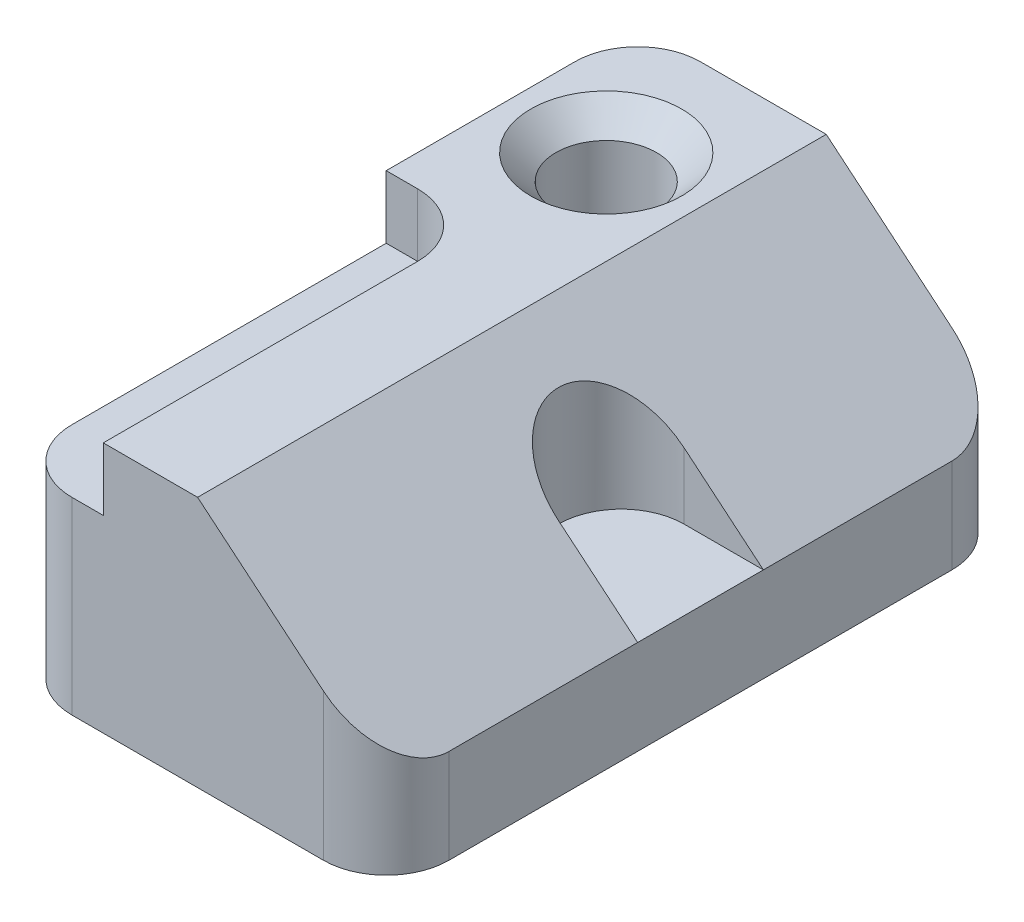
SolidWorks part; units mm, degrees
material "Plain Carbon Steel"
ref_plane "Front Plane" through (0, 0, 0) normal (0, 0, 1) x (1, 0, 0)
ref_plane "Top Plane" through (0, 0, 0) normal (0, 1, 0) x (1, 0, 0)
ref_plane "Right Plane" through (0, 0, 0) normal (1, 0, 0) x (0, 0, -1)
sketch "Sketch1" plane through (0, 0, 0) normal (0, 0, 1) x (1, 0, 0)
  line L0 (0, 0) -> (0, 50.8)
  line L1 (0, 50.8) -> (38.1, 50.8)
  line L2 (38.1, 50.8) -> (76.2, 19.05)
  line L3 (76.2, 19.05) -> (76.2, 0)
  line L4 (76.2, 0) -> (0, 0)
  dimension "D1" = 50.8
  dimension "D2" = 76.2
  dimension "D3" = 19.05
  dimension "D4" = 38.1
extrude "Boss-Extrude1" add sketch "Sketch1" along normal blind 127 contours L4 L0 L1 L2 L3
sketch "Sketch3" plane through (0, 50.8, 0) normal (0, 1, 0) x (1, 0, 0)
  line L0 (0, 0) -> (38.1, 0) construction
  line L1 (0, -127) -> (0, 0) construction
  circle A1 centre (19.05, -25.4) radius 10.16
  point P2 (18.6084, -21.3515)
  point P5 (19.05, 0)
  point P6 (0, 0)
  point P9 (0, 0)
  dimension "D1" = 20.32
  dimension "D2" = 25.4
  dimension "D3" = 19.05
extrude "Cut-Extrude1" cut sketch "Sketch3" against normal blind 127
chamfer "Chamfer1" distance 5.08 angle 45 1 edges at (19.05, 50.8, 35.56)
sketch "Sketch4" plane through (0, 50.8, 0) normal (0, 1, 0) x (1, 0, 0)
  line L1 (0, -127) -> (19.05, -127)
  line L2 (0, -127) -> (0, -50.8)
  line L3 (0, -50.8) -> (19.05, -50.8)
  line L4 (19.05, -127) -> (19.05, -50.8)
  dimension "D1" = 76.2
  dimension "D2" = 19.05
extrude "Cut-Extrude3" cut sketch "Sketch4" along direction (0, 1, 0) on the side against the normal blind 12.7 and the other way through all
fillet "Fillet1" radius 12.7 1 edges at (19.05, 44.45, 50.8)
sketch "Sketch5" plane through (0, 50.8, 0) normal (0, 1, 0) x (1, 0, 0)
  line L0 (38.1, -63.5) -> (76.2, -63.5) construction
  line L1 (38.1, -127) -> (38.1, 0) construction
  line L2 (76.2, -127) -> (76.2, 0) construction
  line L3 (76.2, -50.8) -> (60.198, -50.8)
  line L4 (76.2, -76.2) -> (60.198, -76.2)
  line L5 (76.2, -50.8) -> (76.2, -76.2)
  arc A0 (60.198, -50.8) -> (60.198, -76.2) centre (60.198, -63.5) ccw
  dimension "D2" = 16.002
  dimension "D1" = 12.7
  dimension "D3" = 16.002
extrude "Cut-Extrude4" cut sketch "Sketch5" against normal up to vertex (31.75 mm away)
fillet "Fillet2" radius 12.7 1 edges at (0, 19.05, 127)
fillet "Fillet3" radius 12.7 1 edges at (76.2, 9.525, 127)
fillet "Fillet4" radius 12.7 1 edges at (76.2, 9.525, 0)
fillet "Fillet5" radius 12.7 1 edges at (0, 25.4, 0)
